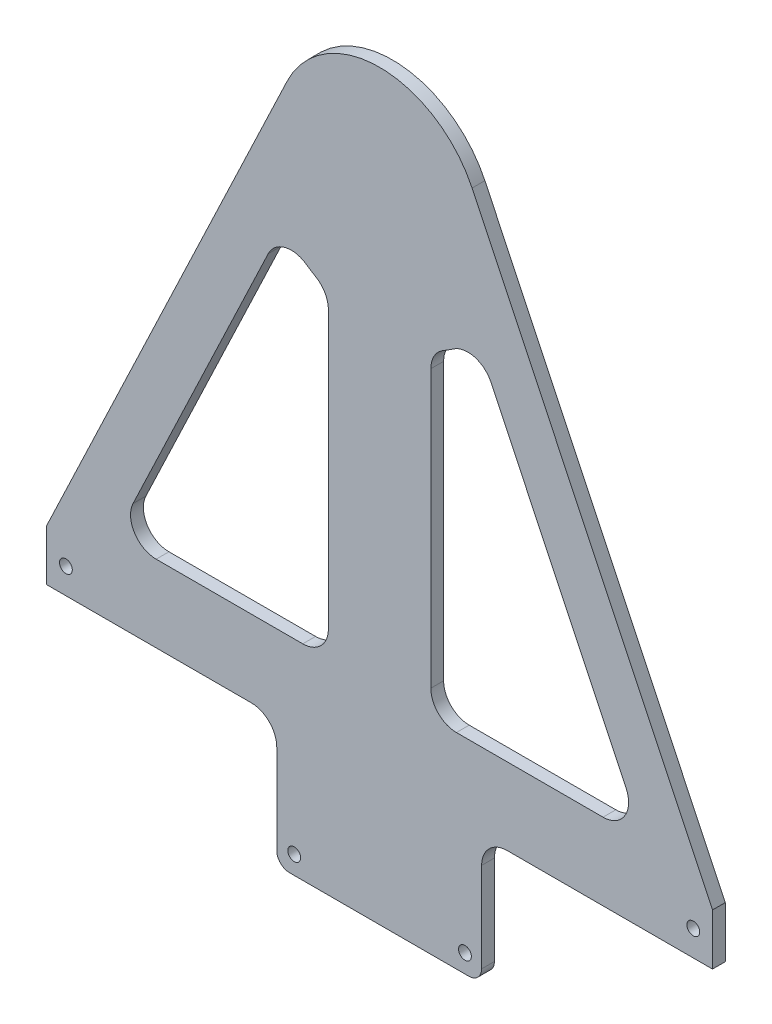
SolidWorks part; units mm, degrees
material "Titanium Ti-5Al-2.5Sn"
ref_plane "Front Plane" through (0, 0, 0) normal (0, 0, 1) x (1, 0, 0)
ref_plane "Top Plane" through (0, 0, 0) normal (0, 1, 0) x (1, 0, 0)
ref_plane "Right Plane" through (0, 0, 0) normal (1, 0, 0) x (0, 0, -1)
sketch "Sketch1" plane through (0, 0, 0) normal (0, 0, 1) x (1, 0, 0)
  line L0 (0, -58.42) -> (0, 58.42) construction
  line L2 (-82.55, 55.7897) -> (-82.55, -52.07)
  line L3 (-76.2, -58.42) -> (76.2, -58.42)
  line L4 (82.55, 55.7897) -> (82.55, -52.07)
  line L5 (-82.55, 58.42) -> (82.55, -58.42) construction
  line L6 (-82.55, -58.42) -> (82.55, 58.42) construction
  line L7 (-80.6901, 60.2799) -> (-75.4296, 65.5404)
  line L8 (-70.9395, 67.4003) -> (-50.8, 67.4003)
  line L9 (-46.3099, 65.5404) -> (-41.0494, 60.2799)
  line L10 (46.3099, 65.5404) -> (41.0494, 60.2799)
  line L11 (70.9395, 67.4003) -> (50.8, 67.4003)
  line L12 (80.6901, 60.2799) -> (75.4296, 65.5404)
  line L13 (-73.5697, 67.4003) -> (-82.55, 67.4003) construction
  line L14 (-82.55, 67.4003) -> (-82.55, 58.42) construction
  line L15 (-36.5592, 58.42) -> (0, 58.42)
  line L16 (0, 58.42) -> (36.5592, 58.42)
  circle A0 centre (-77.7875, -35.052) radius 1.5875
  circle A1 centre (-77.7875, -11.684) radius 1.5875
  circle A2 centre (-77.7875, 11.684) radius 1.5875
  circle A3 centre (-77.7875, 35.052) radius 1.5875
  circle A4 centre (77.7875, 35.052) radius 1.5875
  circle A5 centre (77.7875, 11.684) radius 1.5875
  circle A6 centre (77.7875, -11.684) radius 1.5875
  circle A7 centre (77.7875, -35.052) radius 1.5875
  arc A8 (82.55, 55.7897) -> (80.6901, 60.2799) centre (76.2, 55.7897) ccw
  arc A9 (75.4296, 65.5404) -> (70.9395, 67.4003) centre (70.9395, 61.0503) ccw
  arc A10 (46.3099, 65.5404) -> (50.8, 67.4003) centre (50.8, 61.0503) cw
  arc A11 (41.0494, 60.2799) -> (36.5592, 58.42) centre (36.5592, 64.77) cw
  arc A12 (-36.5592, 58.42) -> (-41.0494, 60.2799) centre (-36.5592, 64.77) cw
  arc A13 (-46.3099, 65.5404) -> (-50.8, 67.4003) centre (-50.8, 61.0503) ccw
  arc A14 (-70.9395, 67.4003) -> (-75.4296, 65.5404) centre (-70.9395, 61.0503) ccw
  arc A15 (-82.55, 55.7897) -> (-80.6901, 60.2799) centre (-76.2, 55.7897) cw
  arc A16 (76.2, -58.42) -> (82.55, -52.07) centre (76.2, -52.07) ccw
  arc A17 (-76.2, -58.42) -> (-82.55, -52.07) centre (-76.2, -52.07) cw
  circle A18 centre (-70.9395, 61.0503) radius 1.5875
  circle A19 centre (-50.8, 61.0503) radius 1.5875
  circle A20 centre (50.8, 61.0503) radius 1.5875
  circle A21 centre (70.9395, 61.0503) radius 1.5875
  point P0 (0, 0)
  point P36 (73.5697, 67.4003)
  point P39 (48.1697, 67.4003)
  point P42 (39.1895, 58.42)
  point P45 (-39.1895, 58.42)
  point P48 (-48.1697, 67.4003)
  dimension "D3" = 3.175
  dimension "D11" = 6.35
  dimension "D12" = 6.35
  dimension "D13" = 3.175
  dimension "D14" = 3.175
  dimension "D1" = 165.1
  dimension "D2" = 116.84
  dimension "D4" = 23.368
  dimension "D5" = 4.7625
  dimension "D7" = 46.736
  dimension "D8" = 12.7
  dimension "D9" = 135
  dimension "D10" = 25.4
  dimension "D6" = 4
extrude "Boss-Extrude1" [suppressed] add sketch "Sketch1" along normal blind 1.5
sketch "Sketch2" [suppressed] plane through (0, 0, 1.5) normal (0, 0, 1) x (1, 0, 0)
  line L0 (0, -45.72) -> (0, 6.3634) construction
  line L1 (0, -58.42) -> (0, 63.5) construction
  line L3 (-82.55, 1.8599) -> (82.55, 1.8599) construction
  line L4 (-82.55, 55.7897) -> (-82.55, -52.07) construction
  line L5 (82.55, -52.07) -> (82.55, 55.7897) construction
  line L7 (-76.2, -58.42) -> (76.2, -58.42) construction
  circle A0 centre (0, -45.72) radius 1.9062
  circle A1 centre (0, 6.3634) radius 1.9062
  dimension "D2" = 3.8125
  dimension "D3" = 3.8125
  dimension "D1" = 52.0834
  dimension "D4" = 12.7
extrude "Cut-Extrude1" [suppressed] cut sketch "Sketch2" against normal through all
sketch "Sketch3" [suppressed] plane through (0, 0, 1.5) normal (0, 0, 1) x (1, 0, 0)
  line L0 (0, 50.8) -> (0, 30.8) construction
  line L1 (-10, 40.8) -> (10, 40.8) construction
  line L2 (-10, 40.8) -> (0, 50.8) construction
  line L3 (0, 50.8) -> (10, 40.8) construction
  line L4 (10, 40.8) -> (0, 30.8) construction
  line L5 (0, 30.8) -> (-10, 40.8) construction
  line L6 (0, 63.5) -> (0, -58.42) construction
  line L8 (-76.2, -58.42) -> (76.2, -58.42) construction
  circle A0 centre (0, 50.8) radius 1.8669
  circle A1 centre (-10, 40.8) radius 1.8669
  circle A2 centre (0, 30.8) radius 1.8669
  circle A3 centre (10, 40.8) radius 1.8669
  dimension "D1" = 3.7338
  dimension "D2" = 12.7
extrude "Cut-Extrude2" [suppressed] cut sketch "Sketch3" against normal through all
sketch "Sketch4" [suppressed] plane through (0, 0, 1.5) normal (0, 0, 1) x (1, 0, 0)
  line L0 (0, 58.42) -> (0, -58.42) construction
  line L1 (36.5592, 58.42) -> (-36.5592, 58.42) construction
  line L2 (-76.2, -58.42) -> (76.2, -58.42) construction
  line L5 (0, 33.045) -> (0, 52.045) construction
  line L6 (-9.5, 42.545) -> (9.5, 42.545) construction
  circle A14 centre (0, 42.545) radius 8 construction
  circle A15 centre (0, 42.545) radius 9.5 construction
  circle A16 centre (0, 50.545) radius 1.5
  circle A17 centre (0, 34.545) radius 1.5
  circle A18 centre (-9.5, 42.545) radius 1.5
  circle A19 centre (9.5, 42.545) radius 1.5
  dimension "D1" = 15.875
  dimension "D3" = 16
  dimension "D4" = 19
  dimension "D5" = 3
  dimension "D6" = 3
  dimension "D7" = 3
  dimension "D8" = 3
extrude "Cut-Extrude3" [suppressed] cut sketch "Sketch4" against normal through all
sketch "Sketch5" plane through (0, 0, 0) normal (0, 0, 1) x (1, 0, 0)
  line L0 (0, 58.42) -> (0, 13.97) construction
  line L1 (-82.55, 58.42) -> (82.55, 58.42) construction
  line L2 (-82.55, 58.42) -> (-82.55, 45.72)
  line L4 (82.55, 58.42) -> (82.55, 45.72)
  line L5 (82.55, 58.42) -> (22.9335, 183.6386)
  line L8 (77.7875, 45.72) -> (77.7875, 58.42) construction
  line L11 (0, -48.26) -> (0, -46.3538) construction
  line L12 (0, 58.42) -> (0, 172.72) construction
  line L14 (-82.55, 45.72) -> (-31.849, 45.72)
  line L15 (-22.324, 13.97) -> (22.126, 13.97)
  line L16 (-25.499, 17.145) -> (-25.499, 39.37)
  line L17 (25.301, 17.145) -> (25.301, 39.37)
  line L18 (31.651, 45.72) -> (82.55, 45.72)
  line L19 (-82.55, 58.42) -> (-22.9335, 183.6386)
  line L20 (-77.7875, 45.72) -> (-77.7875, 58.42) construction
  line L23 (0, -0.6801) -> (0, 0) construction
  line L24 (0, 13.97) -> (0, 58.42) construction
  line L26 (0, 58.42) -> (-82.55, 58.42) construction
  line L27 (-61.138, 73.8497) -> (-27.6156, 144.2603)
  line L28 (0, -48.26) -> (0, -46.3538) construction
  line L37 (68.4841, 58.42) -> (11.4667, 178.1793) construction
  line L38 (31.651, 58.42) -> (68.4841, 58.42) construction
  line L39 (12.601, 26.67) -> (12.601, 39.37) construction
  line L40 (-12.799, 26.67) -> (12.601, 26.67) construction
  line L41 (-12.799, 26.67) -> (-12.799, 39.37) construction
  line L42 (-68.4841, 58.42) -> (-31.849, 58.42) construction
  line L43 (-12.7, 71.12) -> (-12.7, 139.7244)
  line L44 (-68.4841, 58.42) -> (-11.4667, 178.1793) construction
  line L45 (68.4841, 58.42) -> (68.4841, 58.42) construction
  line L46 (-55.4047, 64.77) -> (-19.05, 64.77)
  line L47 (-12.7, 58.42) -> (-12.7, 172.72) construction
  line L48 (19.05, 64.77) -> (55.4047, 64.77) construction
  line L49 (-82.55, 64.77) -> (82.55, 64.77) construction
  line L50 (-68.4841, 58.42) -> (-68.4841, 58.42) construction
  line L51 (61.138, 73.8497) -> (27.6156, 144.2603)
  line L52 (55.4047, 64.77) -> (19.05, 64.77)
  line L53 (12.7, 71.12) -> (12.7, 139.7244)
  circle A10 centre (21.1667, 18.525) radius 1.5875
  circle A11 centre (-21.1667, 18.525) radius 1.5875
  arc A12 (-25.499, 39.37) -> (-31.849, 45.72) centre (-31.849, 39.37) ccw
  arc A13 (25.301, 39.37) -> (31.651, 45.72) centre (31.651, 39.37) cw
  arc A14 (25.301, 17.145) -> (22.126, 13.97) centre (22.126, 17.145) cw
  arc A15 (-25.499, 17.145) -> (-22.324, 13.97) centre (-22.324, 17.145) ccw
  circle A16 centre (-77.7875, 52.07) radius 1.5875
  circle A17 centre (77.7875, 52.07) radius 1.5875
  arc A18 (22.9335, 183.6386) -> (-22.9335, 183.6386) centre (0, 172.72) ccw
  circle A19 centre (0, 172.72) radius 25.4 construction
  arc A25 (11.4667, 178.1793) -> (-11.4667, 178.1793) centre (0, 172.72) ccw construction
  arc A26 (12.601, 39.37) -> (31.651, 58.42) centre (31.651, 39.37) cw construction
  arc A27 (-12.799, 39.37) -> (-31.849, 58.42) centre (-31.849, 39.37) ccw construction
  arc A28 (12.601, 26.67) -> (12.601, 26.67) centre (12.601, 26.67) cw construction
  arc A29 (-12.799, 26.67) -> (-12.799, 26.67) centre (-12.799, 26.67) ccw construction
  arc A30 (-18.2352, 146.7288) -> (-15.875, 145.2237) centre (0, 172.72) ccw
  arc A31 (-18.2352, 146.7288) -> (-27.6156, 144.2603) centre (-21.8822, 141.5306) ccw
  circle A32 centre (0, 172.72) radius 31.75 construction
  arc A33 (-15.875, 145.2237) -> (-12.7, 139.7244) centre (-19.05, 139.7244) cw
  arc A34 (-19.05, 64.77) -> (-12.7, 71.12) centre (-19.05, 71.12) ccw
  arc A35 (-55.4047, 64.77) -> (-61.138, 73.8497) centre (-55.4047, 71.12) cw
  arc A36 (15.875, 145.2237) -> (12.7, 139.7244) centre (19.05, 139.7244) ccw
  arc A37 (18.2352, 146.7288) -> (15.875, 145.2237) centre (0, 172.72) cw
  arc A38 (18.2352, 146.7288) -> (27.6156, 144.2603) centre (21.8822, 141.5306) cw
  arc A39 (55.4047, 64.77) -> (61.138, 73.8497) centre (55.4047, 71.12) ccw
  arc A40 (19.05, 64.77) -> (12.7, 71.12) centre (19.05, 71.12) cw
  point P0 (0, 0)
  point P37 (0, 0)
  point P52 (25.301, 45.72)
  point P55 (25.301, 13.97)
  point P58 (-25.499, 13.97)
  point P61 (0, 0)
  point P62 (0, 0)
  point P68 (30.3627, 182.0028)
  dimension "D12" = 3.175
  dimension "D13" = 3.175
  dimension "D17" = 6.35
  dimension "D18" = 6.35
  dimension "D19" = 3.175
  dimension "D20" = 3.175
  dimension "D21" = 3.175
  dimension "D4" = 50.8
  dimension "D24" = 6.35
  dimension "D8" = 39.895
  dimension "D9" = 39.895
  dimension "D10" = 61.3833
  dimension "D11" = 61.3833
  dimension "D14" = 12.7
  dimension "D15" = 50.8
  dimension "D16" = 31.75
  dimension "D22" = 6.35
  dimension "D3" = 114.3
  dimension "D5" = 12.7
  dimension "D6" = 6.35
  dimension "D7" = 12.7
  dimension "D23" = 6.35
extrude "Boss-Extrude2" add sketch "Sketch5" along normal blind 3.175
equation "\"Top Plate Width\" = 4.5in"
equation "\"Plate Width\" = 4.6in"
equation "\"Plate Thickness\" = 0.375in"
equation "\"Num holes\" = 4"
equation "\"Plate Height\" = 1.25in"
equation "\"Plate Clearance Hole Diameter\" = 0.125in"
equation "\"D3@Sketch1\"=\"Plate Clearance Hole Diameter\""
equation "\"Hole Spacing\"= \"Plate Width\" / ( \"Num holes\" + 1 )"
equation "\"Plate Tap Hole Diameter\" = 0.116in"
equation "\"Bottom Plate Length\" = 6.5in"
equation "\"D12@Sketch5\"=\"Plate Clearance Hole Diameter\""
equation "\"D13@Sketch5\"=\"Plate Clearance Hole Diameter\""
equation "\"D21@Sketch5\"=\"Plate Clearance Hole Diameter\""
equation "\"Number Eight Clearance Size\" = 0.177in"
equation "\"Back Brace Height\" = 1.1962912in"
equation "\"Titanium Offset Length\" = 4.5in"
equation "\"Titanium Head Radius\" = 2in"
equation "\"D3@Sketch5\"=\"Titanium Offset Length\""
equation "\"D4@Sketch5\"=\"Titanium Head Radius\""
equation "\"Titanium Plate Border Thickness\" = 0.5in"
equation "\"D5@Sketch5\"=\"Titanium Plate Border Thickness\""
equation "\"D6@Sketch5\"=\"Titanium Plate Border Thickness\" / 2"
equation "\"D23@Sketch5\"=\"Titanium Plate Border Thickness\"/2"
